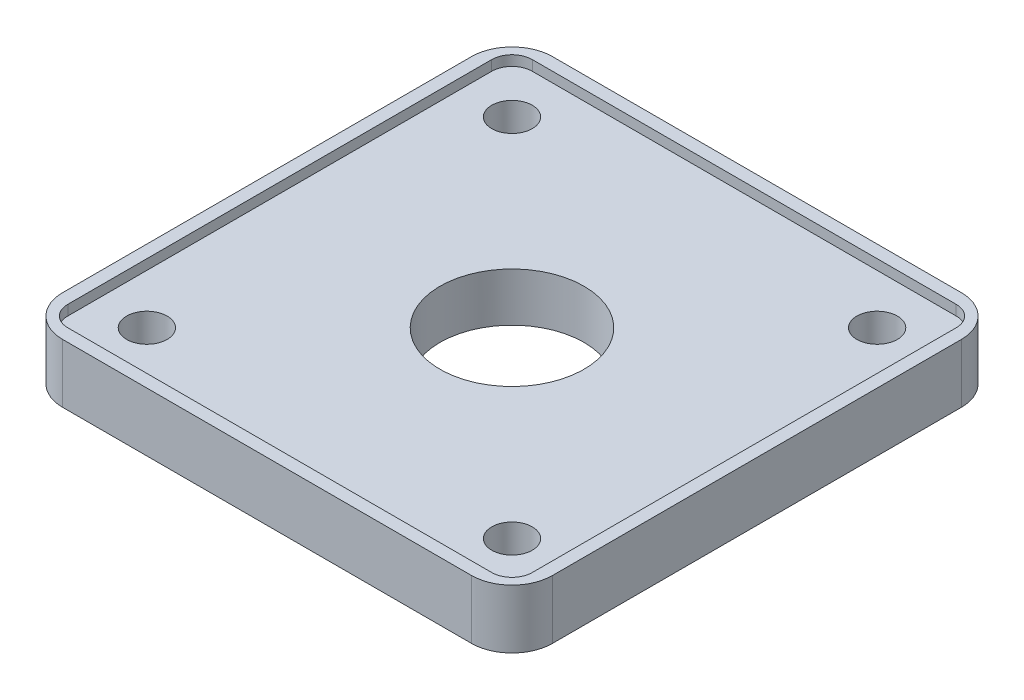
SolidWorks part; units mm, degrees
ref_plane "Ön Düzlem" through (0, 0, 0) normal (0, 0, 1) x (1, 0, 0)
ref_plane "Üst Düzlem" through (0, 0, 0) normal (0, 1, 0) x (1, 0, 0)
ref_plane "Sağ Düzlem" through (0, 0, 0) normal (1, 0, 0) x (0, 0, -1)
sketch "Çizim1" plane through (0, 0, 0) normal (0, 1, 0) x (1, 0, 0)
  line L1 (-20.15, -24.15) -> (20.15, -24.15)
  line L2 (-24.15, -20.15) -> (-24.15, 20.15)
  line L3 (-20.15, 24.15) -> (20.15, 24.15)
  line L4 (24.15, -20.15) -> (24.15, 20.15)
  line L5 (-24.15, -24.15) -> (24.15, 24.15) construction
  line L6 (-24.15, 24.15) -> (24.15, -24.15) construction
  circle A0 centre (0, 0) radius 7.1
  circle A1 centre (-18, 18) radius 2
  circle A2 centre (-18, -18) radius 2
  circle A3 centre (18, -18) radius 2
  circle A4 centre (18, 18) radius 2
  arc A5 (20.15, -24.15) -> (24.15, -20.15) centre (20.15, -20.15) ccw
  arc A6 (-20.15, -24.15) -> (-24.15, -20.15) centre (-20.15, -20.15) cw
  arc A7 (20.15, 24.15) -> (24.15, 20.15) centre (20.15, 20.15) cw
  arc A8 (-24.15, 20.15) -> (-20.15, 24.15) centre (-20.15, 20.15) cw
  point P0 (0, 0)
  dimension "D2" = 14.2
  dimension "D3" = 4
  dimension "D6" = 36
  dimension "D7" = 4
  dimension "D1" = 48.3
  dimension "D4" = 36
  dimension "D5" = 18
extrude "Yükseklik-Ekstrüzyon1" add sketch "Çizim1" along normal blind 5.8
sketch "Çizim2" plane through (0, 5.8, 0) normal (0, 1, 0) x (1, 0, 0)
  line L1 (-20.9, -22.9) -> (20.9, -22.9)
  line L2 (-22.9, -20.9) -> (-22.9, 20.9)
  line L3 (-20.9, 22.9) -> (20.9, 22.9)
  line L4 (22.9, -20.9) -> (22.9, 20.9)
  line L5 (-22.9, -22.9) -> (22.9, 22.9) construction
  line L6 (-22.9, 22.9) -> (22.9, -22.9) construction
  arc A0 (20.9, 22.9) -> (22.9, 20.9) centre (20.9, 20.9) cw
  arc A1 (20.9, -22.9) -> (22.9, -20.9) centre (20.9, -20.9) ccw
  arc A2 (-20.9, -22.9) -> (-22.9, -20.9) centre (-20.9, -20.9) cw
  arc A3 (-22.9, 20.9) -> (-20.9, 22.9) centre (-20.9, 20.9) cw
  point P0 (0, 0)
  dimension "D2" = 2
  dimension "D1" = 45.8
extrude "Kes-Ekstrüzyon1" cut sketch "Çizim2" against normal blind 1
